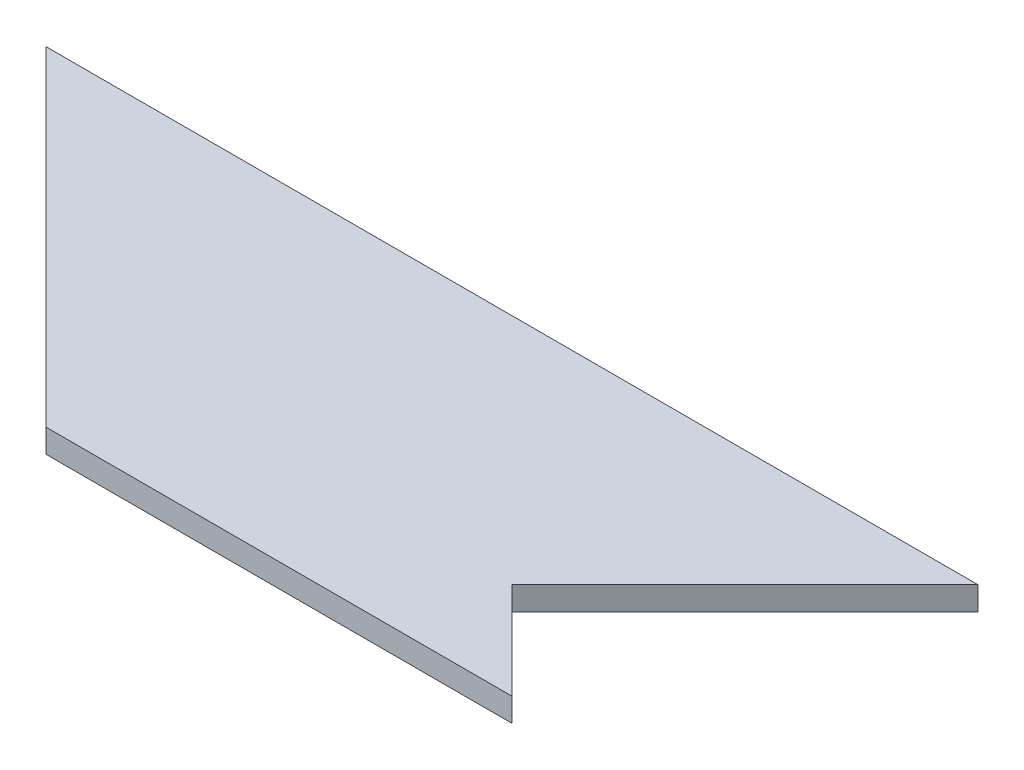
SolidWorks part; units mm, degrees
ref_plane "Front Plane" through (0, 0, 0) normal (0, 0, 1) x (1, 0, 0)
ref_plane "Top Plane" through (0, 0, 0) normal (0, 1, 0) x (1, 0, 0)
ref_plane "Right Plane" through (0, 0, 0) normal (1, 0, 0) x (0, 0, -1)
sketch "Sketch2" plane through (0, 0, 0) normal (0, 1, 0) x (1, 0, 0)
  line L0 (-59.4, 16.2379) -> (-17.3979, -25.7643)
  line L1 (-59.4, 16.2379) -> (59.4, 16.2379)
  line L3 (-17.3979, -25.7643) -> (42.0021, -25.7643)
  line L7 (59.4, 16.2379) -> (29.7015, -13.4606)
  line L8 (29.7015, -13.4606) -> (42.0021, -25.7643)
  point P0 (0, 0)
  dimension "D1" = 118.8
  dimension "D2" = 45
  dimension "D3" = 45
  dimension "D4" = 59.4
  dimension "D5" = 42
  dimension "D6" = 59.4
  dimension "D7" = 17.3979
extrude "Boss-Extrude1" add sketch "Sketch2" along normal blind 3
